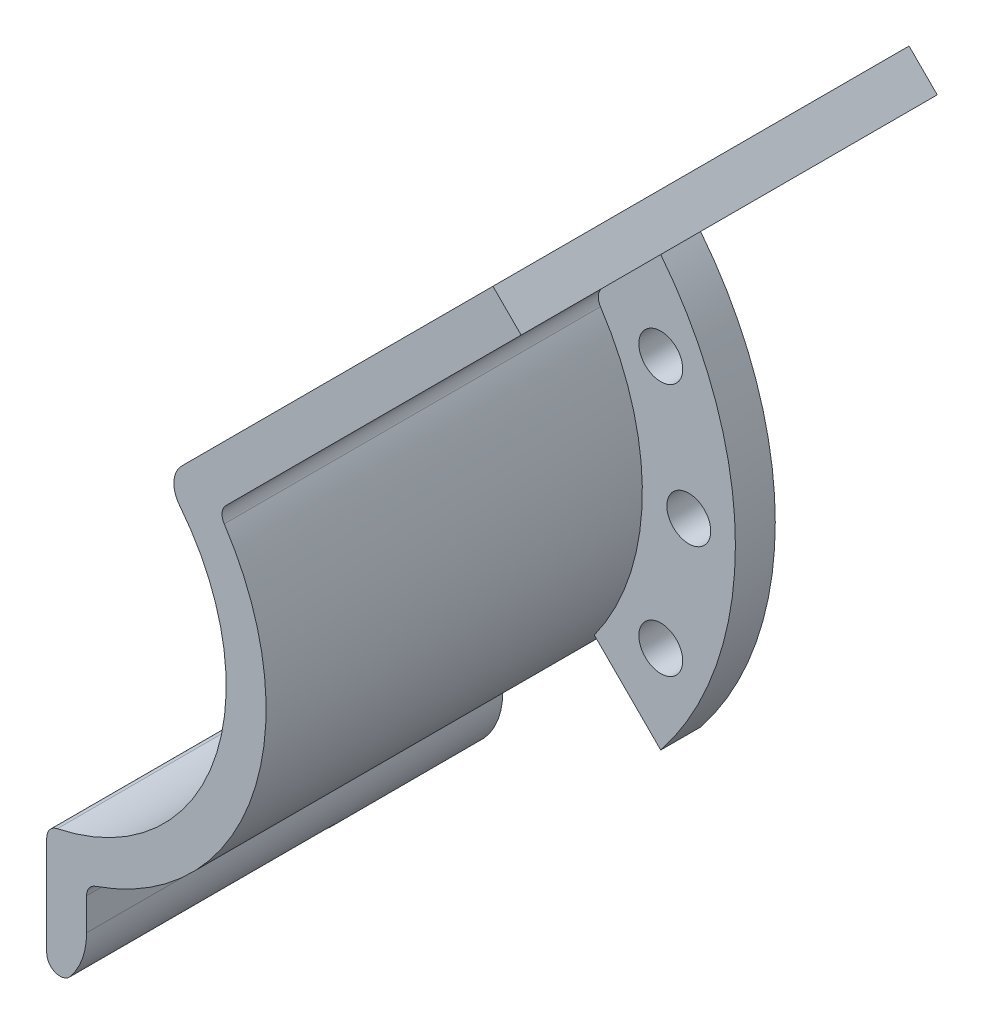
SolidWorks part; units mm, degrees
ref_plane "前视基准面" through (0, 0, 0) normal (0, 0, 1) x (1, 0, 0)
ref_plane "上视基准面" through (0, 0, 0) normal (0, 1, 0) x (1, 0, 0)
ref_plane "右视基准面" through (0, 0, 0) normal (1, 0, 0) x (0, 0, -1)
sketch "草图1" plane through (0, 0, -1.3) normal (0, 0, 1) x (1, 0, 0)
  line L0 (36.0624, 36.0624) -> (11.3137, 11.3137)
  line L1 (0, 23.564) -> (0, -22.8784) construction
  line L2 (11.3137, 11.3137) -> (36.0624, 36.0624) construction
  line L3 (2.5, -15.8035) -> (2.5, -18.8348)
  line L4 (1.5, -13.5) -> (1.5, -14.3614) construction
  line L5 (36.0624, 36.0624) -> (38.1838, 33.9411)
  line L6 (38.1838, 33.9411) -> (15.3878, 11.1452)
  arc A0 (11.9682, -9.0422) -> (14.8566, -2.069) centre (0, 0) ccw construction
  arc A2 (2.5, -18.8348) -> (15.3878, 11.1452) centre (0, 0) ccw
  arc A3 (2.5, -15.8035) -> (11.3137, 11.3137) centre (0, 0) ccw
  point P20 (1.5, -13.9307)
  dimension "D1" = 1
  dimension "D4" = 45
  dimension "D2" = 3
  dimension "D3" = 35
  dimension "D5" = 1
  dimension "D6" = 3
  dimension "D7" = 35
extrude "凸台-拉伸1" add sketch "草图1" along normal up to surface (31.3 mm away)
sketch "草图2" plane through (0, 0, -1.3) normal (0, 0, 1) x (1, 0, 0)
  line L0 (15.3878, 11.1452) -> (38.1838, 33.9411) construction
  line L1 (0, 0) -> (31.8729, 0) construction
  line L2 (15.3878, 11.1452) -> (38.1838, 33.9411) construction
  line L3 (15.3878, 11.1452) -> (20.3833, 16.1407)
  line L4 (15.3878, -11.1452) -> (20.3833, -16.1407)
  arc A0 (20.3833, 16.1407) -> (20.3833, -16.1407) centre (0, 0) cw
  arc A2 (2.5, -18.8348) -> (15.3878, 11.1452) centre (0, 0) ccw construction
  arc A3 (15.3878, -11.1452) -> (15.3878, 11.1452) centre (0, 0) ccw
  arc A4 (17.8856, -13.6429) -> (17.8856, 13.6429) centre (0, 0) ccw construction
  dimension "D1" = 26
extrude "凸台-拉伸2" add sketch "草图2" along normal blind 3
sketch "草图8" plane through (0, 0, -1.3) normal (0, 0, 1) x (1, 0, 0)
  line L0 (2.5, -18.8348) -> (2.5, -21.3348)
  line L1 (0, -23.8348) -> (0, -26.8348)
  line L2 (5.5, -21.3348) -> (5.5, -18.1865)
  line L3 (2.5, -21.3348) -> (-1.9026, -21.3348) construction
  line L4 (0, -23.8348) -> (0, -21.3348) construction
  arc A0 (2.5, -21.3348) -> (0, -23.8348) centre (0, -21.3348) cw
  arc A1 (0, -26.8348) -> (5.5, -21.3348) centre (0, -21.3348) ccw
  arc A2 (2.5, -18.8348) -> (15.3878, 11.1452) centre (0, 0) ccw construction
  arc A4 (2.5, -18.8348) -> (15.3878, -11.1452) centre (0, 0) ccw construction
  arc A5 (2.5, -18.8348) -> (5.5, -18.1865) centre (0, 0) ccw
  dimension "D1" = 3
  dimension "D4" = 2.5
  dimension "D2" = 3
  dimension "D3" = 2.5
extrude "凸台-拉伸3" add sketch "草图8" along normal up to surface (31.3 mm away) up to face at (20.4615, 8.5774, 30)
sketch "草图9" plane through (0, 0, 30) normal (0, 0, 1) x (1, 0, 0)
  line L0 (2.5, -15.8035) -> (2.5, -21.3348) construction
  line L1 (-5.2306, -21.3348) -> (2.5, -21.3348)
  line L2 (-5.2306, -21.3348) -> (-5.2306, -27.3309)
  line L3 (-5.2306, -27.3309) -> (2.5, -27.3309)
  line L4 (2.5, -21.3348) -> (2.5, -27.3309)
extrude "切除-拉伸1" cut sketch "草图9" against normal blind 20
hole_wizard "ST2.9 间隙孔1" positions "草图6" profile "草图7" hole size "ST2.9" standard "GB" end condition through all
sketch "草图6" plane through (0, 0, 1.7) normal (0, 0, 1) x (1, 0, 0)
  line L0 (15.3878, -11.1452) -> (20.3833, -16.1407) construction
  line L1 (15.3878, 11.1452) -> (38.1838, 33.9411) construction
  line L2 (0, 0) -> (22.4949, 0) construction
  line L4 (0, 0) -> (20.3873, 9.5068) construction
  line L6 (0, 0) -> (20.3873, -9.5068) construction
  arc A0 (17.8856, -13.6429) -> (17.8856, 13.6429) centre (0, 0) ccw construction
  point P0 (22.4949, 0)
  point P14 (20.3873, 9.5068)
  point P16 (20.3873, -9.5068)
  dimension "D1" = 25
  dimension "D2" = 25
sketch "草图7" plane through (22.4949, 0, 1.7) normal (1, 0, 0) x (0, -1, 0)
  line L0 (0, 0) -> (0, 3)
  line L1 (0, 3) -> (1.65, 3)
  line L2 (1.65, 3) -> (1.65, 0)
  line L5 (1.65, 0) -> (0, 0)
  line L11 (0, -6.35) -> (0, 107.95) construction
  dimension "通孔孔直径" = 3.3
  dimension "通孔孔深度" = 3
fillet "圆角1" radius 1 4 edges at (2.5, -15.8035, 14.35) (15.3878, 11.1452, 15.85) (5.5, -18.1865, 14.35) (2.5, -26.2338, 20)
fillet "圆角2" radius 2 1 edges at (11.3137, 11.3137, 14.35)
